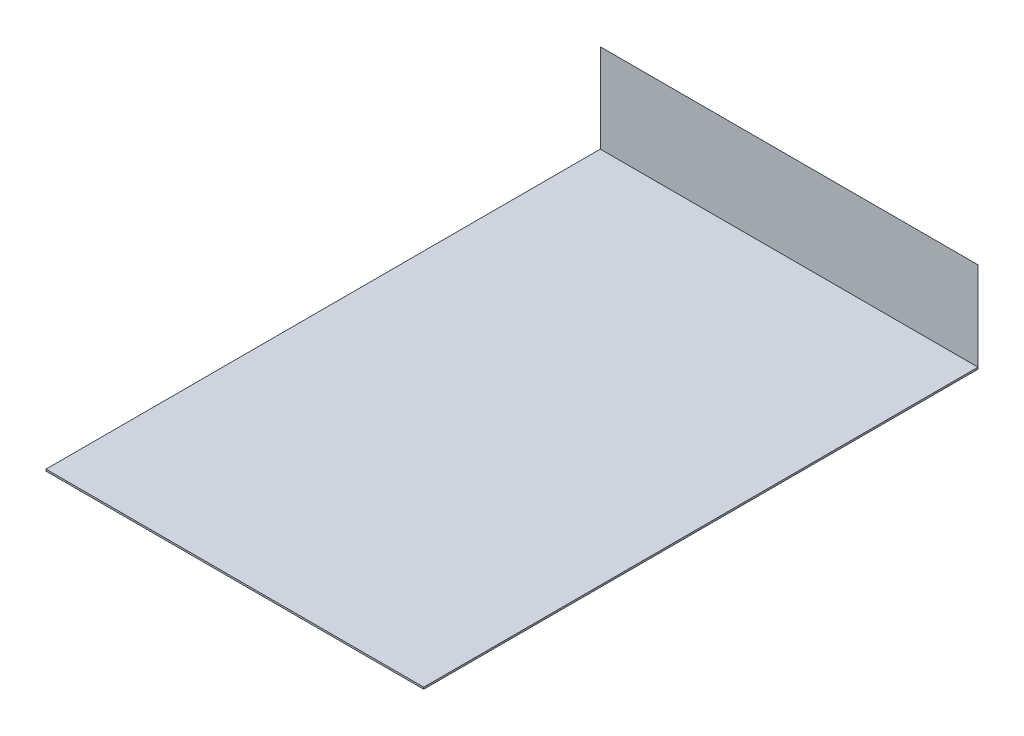
SolidWorks part; units mm, degrees
ref_plane "Front Plane" through (0, 0, 0) normal (0, 0, 1) x (1, 0, 0)
ref_plane "Top Plane" through (0, 0, 0) normal (0, 1, 0) x (1, 0, 0)
ref_plane "Right Plane" through (0, 0, 0) normal (1, 0, 0) x (0, 0, -1)
sketch "Sketch2" plane through (0, 0, 0) normal (0, 1, 0) x (1, 0, 0)
  line L1 (-106.5, 312.59) -> (106.5, 312.59)
  line L2 (-106.5, 312.59) -> (-106.5, 0)
  line L3 (-106.5, 0) -> (106.5, 0)
  line L4 (106.5, 312.59) -> (106.5, 0)
  line L5 (-106.5, 312.59) -> (106.5, 0) construction
  line L6 (-106.5, 0) -> (106.5, 312.59) construction
  point P0 (0, 156.295)
  dimension "D1" = 213
  dimension "D2" = 312.59
extrude "Boss-Extrude1" add sketch "Sketch2" against normal blind 1
sketch "Sketch3" plane through (0, 0, 0) normal (0, 1, 0) x (1, 0, 0)
  line L0 (-106.5, 312.59) -> (106.5, 312.59)
surface "Surface-Extrude1" sketch "Sketch3" parameters "D1"=50
